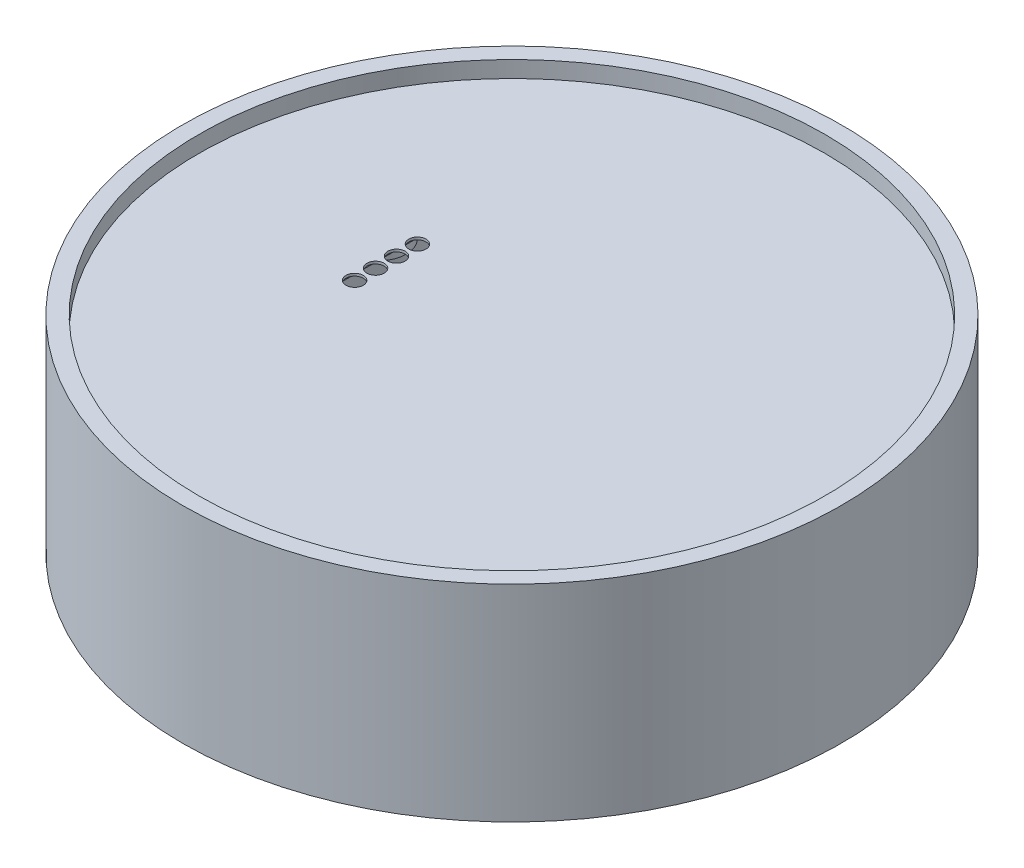
SolidWorks part; units mm, degrees
ref_plane "Front Plane" through (0, 0, 0) normal (0, 0, 1) x (1, 0, 0)
ref_plane "Top Plane" through (0, 0, 0) normal (0, 1, 0) x (1, 0, 0)
ref_plane "Right Plane" through (0, 0, 0) normal (1, 0, 0) x (0, 0, -1)
sketch "Sketch1" plane through (0, 0, 0) normal (0, 1, 0) x (1, 0, 0)
  circle A0 centre (0, 0) radius 40
  dimension "D1" = 80
extrude "Boss-Extrude1" add sketch "Sketch1" against normal blind 25
sketch "Sketch2" plane through (0, 0, 0) normal (0, 1, 0) x (1, 0, 0)
  circle A2 centre (0, 0) radius 38
  circle A3 centre (0, 0) radius 38
  dimension "D1" = 2
extrude "Cut-Extrude1" cut sketch "Sketch2" against normal blind 2
sketch "Sketch3" plane through (0, -25, 0) normal (0, -1, 0) x (1, 0, 0)
  circle A2 centre (0, 0) radius 37
  circle A3 centre (0, 0) radius 37
  dimension "D1" = 3
extrude "Cut-Extrude2" cut sketch "Sketch3" against normal offset from surface (21.5 mm away) 1.5 up to face at (0, -2, 38)
sketch "Sketch4" plane through (0, 0, 0) normal (1, 0, 0) x (0, 0, -1)
  line L0 (40, 0) -> (-40, 0) construction
  line L1 (6.25, -8.2) -> (-6.25, -8.2)
  line L2 (6.25, -8.2) -> (6.25, -19.7)
  line L3 (6.25, -19.7) -> (-6.25, -19.7)
  line L4 (-6.25, -8.2) -> (-6.25, -19.7)
  line L5 (6.25, -8.2) -> (-6.25, -19.7) construction
  line L6 (6.25, -19.7) -> (-6.25, -8.2) construction
  point P0 (0, -13.95)
  dimension "D1" = 11.5
  dimension "D2" = 12.5
  dimension "D3" = 8.2
extrude "Cut-Extrude3" cut sketch "Sketch4" against normal through all
sketch "Sketch5" plane through (0, -2, 0) normal (0, 1, 0) x (1, 0, 0)
  circle A0 centre (-15.2035, 3.7327) radius 1.05
  circle A1 centre (-15.2035, 1.1927) radius 1.05
  circle A2 centre (-15.2035, -1.3473) radius 1.05
  circle A3 centre (-15.2035, -3.8873) radius 1.05
  dimension "D1" = 2.1
extrude "Cut-Extrude4" cut sketch "Sketch5" against normal through all
sketch "Sketch6" plane through (0, -3.5, 0) normal (0, -1, 0) x (1, 0, 0)
  line L0 (-15.2035, -3.7327) -> (-15.2035, 3.8873) construction
  line L1 (-17.3295, -7.7953) -> (-13.0776, -7.7953)
  line L2 (-17.3295, -7.7953) -> (-17.3295, 7.9499)
  line L3 (-17.3295, 7.9499) -> (-13.0776, 7.9499)
  line L4 (-13.0776, -7.7953) -> (-13.0776, 7.9499)
  line L5 (-17.3295, -7.7953) -> (-13.0776, 7.9499) construction
  line L6 (-17.3295, 7.9499) -> (-13.0776, -7.7953) construction
  point P0 (-15.2035, 0.0773)
extrude "Cut-Extrude5" cut sketch "Sketch6" against normal offset from surface (1.2 mm away) 0.3 up to face at (-15.2035, -2, 4.9373)
sketch "Sketch7" plane through (0, -3.5, 0) normal (0, -1, 0) x (1, 0, 0)
  circle A0 centre (-22.144, 6.9382) radius 1.5
  circle A1 centre (-22.144, 6.9382) radius 3.3
  circle A2 centre (-22.4162, -6.2844) radius 1.5
  circle A3 centre (-22.4162, -6.2844) radius 3.3
  dimension "D1" = 1.8
  dimension "D2" = 1.8
extrude "Boss-Extrude2" add sketch "Sketch7" along normal blind 2.8
fillet "Fillet1" radius 1 1 edges at (-22.144, -3.5, 10.2382)
ref_plane "Plane1" through (-40, 0, 0) normal (-1, 0, 0) x (0, 0, 1)
sketch "Sketch8" plane through (-40, 0, 0) normal (-1, 0, 0) x (0, 0, 1)
  line L0 (0, 0) -> (0, -10.1853) construction
  line L1 (-6, -7.9353) -> (6, -7.9353)
  line L2 (-6, -7.9353) -> (-6, -12.4353)
  line L3 (-6, -12.4353) -> (6, -12.4353)
  line L4 (6, -7.9353) -> (6, -12.4353)
  line L5 (-6, -7.9353) -> (6, -12.4353) construction
  line L6 (-6, -12.4353) -> (6, -7.9353) construction
  point P0 (0, -10.1853)
  dimension "D2" = 4.5
  dimension "D3" = 12
extrude "Cut-Extrude6" [suppressed] cut sketch "Sketch8" against normal offset from surface (2.4767 mm away) 1
sketch "Sketch9" plane through (0, -3.5, 0) normal (0, -1, 0) x (1, 0, 0)
  line L0 (0, 0) -> (25.0773, 0) construction
  circle A0 centre (0, 25) radius 3.25
  circle A1 centre (0, 25) radius 4.75
  circle A2 centre (0, -25) radius 3.25
  circle A3 centre (0, -25) radius 4.75
  dimension "D1" = 6.5
  dimension "D3" = 25
  dimension "D2" = 1.5
extrude "Boss-Extrude3" add sketch "Sketch9" along normal blind 6.4
fillet "Fillet2" [suppressed] radius 1
sketch "Sketch10" plane through (0, -3.5, 0) normal (0, -1, 0) x (1, 0, 0)
  circle A0 centre (0, 0) radius 3
  circle A1 centre (0, 0) radius 8
  dimension "D1" = 5
extrude "Boss-Extrude4" add sketch "Sketch10" along normal offset from surface (15.5 mm away) 6 up to face at (0, -25, -37)
fillet "Fillet3" radius 4 1 edges at (0, -3.5, 8)
